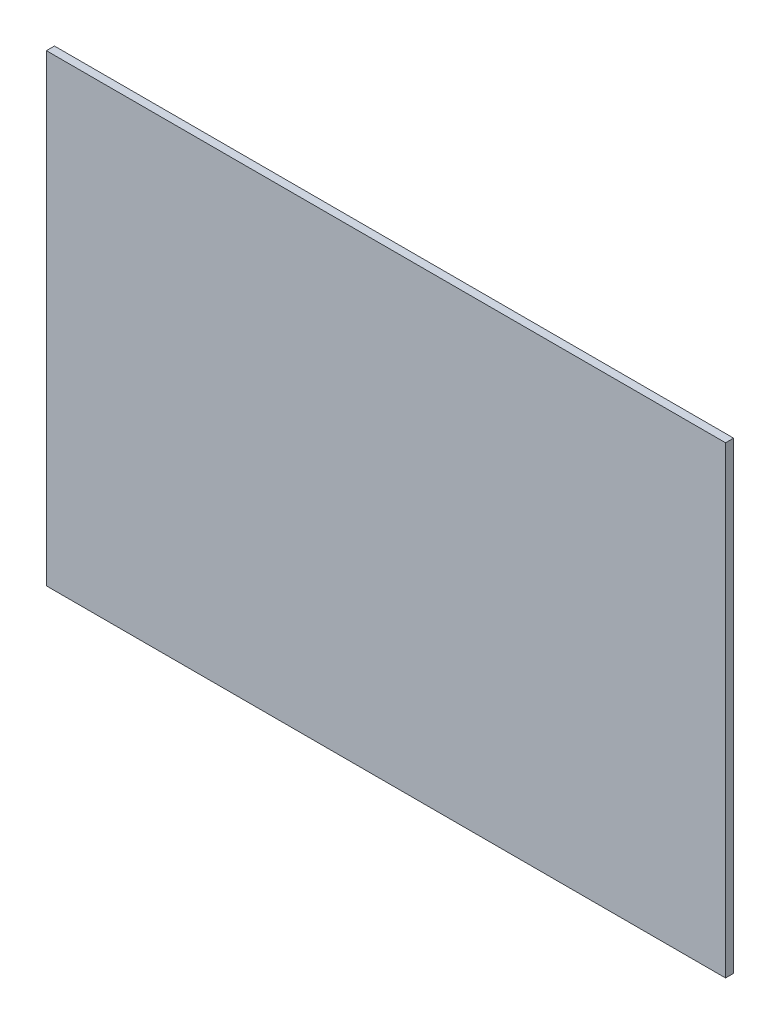
SolidWorks part; units mm, degrees
material "6063-T6"
ref_plane "Front Plane" through (0, 0, 0) normal (0, 0, 1) x (1, 0, 0)
ref_plane "Top Plane" through (0, 0, 0) normal (0, 1, 0) x (1, 0, 0)
ref_plane "Right Plane" through (0, 0, 0) normal (1, 0, 0) x (0, 0, -1)
sketch "Sketch1" plane through (0, 0, 0) normal (0, 0, 1) x (1, 0, 0)
  line L1 (0, 0) -> (337, 0)
  line L2 (0, 0) -> (0, 230)
  line L3 (0, 230) -> (337, 230)
  line L4 (337, 0) -> (337, 230)
  dimension "D1" = 337
  dimension "D2" = 230
extrude "Boss-Extrude1" add sketch "Sketch1" along normal blind 4
